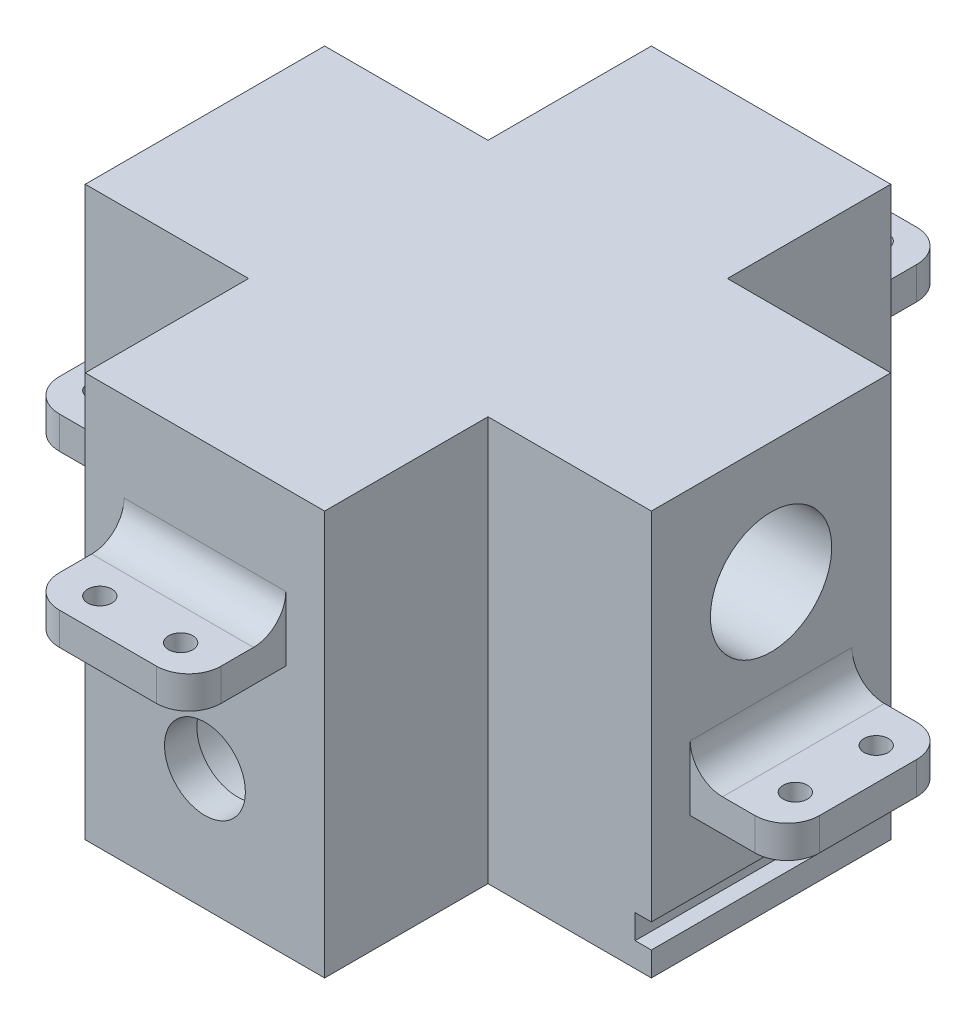
SolidWorks part; units mm, degrees
ref_plane "Plan de face" through (0, 0, 0) normal (0, 0, 1) x (1, 0, 0)
ref_plane "Plan de dessus" through (0, 0, 0) normal (0, 1, 0) x (1, 0, 0)
ref_plane "Plan de droite" through (0, 0, 0) normal (1, 0, 0) x (0, 0, -1)
sketch "Esquisse1" plane through (0, 0, 0) normal (1, 0, 0) x (0, 0, -1)
  line L2 (0, 0) -> (70, 0)
  line L3 (0, 0) -> (0, 50)
  line L4 (0, 50) -> (70, 50)
  line L5 (70, 0) -> (70, 50)
  dimension "D1" = 50
  dimension "D2" = 70
extrude "Boss.-Extru.1" add sketch "Esquisse1" along normal blind 70
sketch "Esquisse2" plane through (0, 0, 0) normal (0, 0, 1) x (1, 0, 0)
  line L0 (70, 0) -> (0, 0) construction
  line L1 (0, 50) -> (0, 0) construction
  circle A0 centre (35, 15) radius 7.5
  dimension "D1" = 15
  dimension "D2" = 15
  dimension "D3" = 35
extrude "Enlèv. mat.-Extru.1" cut sketch "Esquisse2" against normal through all
sketch "Esquisse3" plane through (0, 0, 0) normal (-1, 0, 0) x (0, 0, 1)
  line L0 (-70, 50) -> (0, 50) construction
  line L1 (0, 50) -> (0, 0) construction
  circle A0 centre (-35, 35) radius 7.5
  dimension "D1" = 15
  dimension "D2" = 15
  dimension "D3" = 35
extrude "Enlèv. mat.-Extru.2" cut sketch "Esquisse3" against normal through all
sketch "Esquisse4" plane through (0, 0, 0) normal (0, -1, 0) x (1, 0, 0)
  line L1 (0, -70) -> (20.2, -70)
  line L2 (0, -70) -> (0, -49.8)
  line L3 (0, -49.8) -> (20.2, -49.8)
  line L4 (20.2, -70) -> (20.2, -49.8)
  line L5 (0, 0) -> (20.2, 0)
  line L6 (0, 0) -> (0, -20.2)
  line L7 (0, -20.2) -> (20.2, -20.2)
  line L8 (20.2, 0) -> (20.2, -20.2)
  line L9 (70, 0) -> (49.8, 0)
  line L10 (70, 0) -> (70, -20.2)
  line L11 (70, -20.2) -> (49.8, -20.2)
  line L12 (49.8, 0) -> (49.8, -20.2)
  line L13 (70, -70) -> (49.8, -70)
  line L14 (70, -70) -> (70, -49.8)
  line L15 (70, -49.8) -> (49.8, -49.8)
  line L16 (49.8, -70) -> (49.8, -49.8)
  dimension "D1" = 20.2
  dimension "D2" = 20.2
  dimension "D3" = 20.2
  dimension "D4" = 20.2
  dimension "D5" = 20.2
  dimension "D6" = 20.2
  dimension "D7" = 20.2
  dimension "D8" = 20.2
extrude "Enlèv. mat.-Extru.3" cut sketch "Esquisse4" against normal through all
sketch "Esquisse7" plane through (0, 0, 0) normal (0, 0, 1) x (1, 0, 0)
  circle A0 centre (35, 15) radius 5
  circle A1 centre (35, 15) radius 11.7367
  dimension "D1" = 10
extrude "Boss.-Extru.3" add sketch "Esquisse7" against normal blind 4
sketch "Esquisse8" plane through (0, 0, 0) normal (-1, 0, 0) x (0, 0, 1)
  circle A0 centre (-35, 35) radius 12.1967
  circle A1 centre (-35, 35) radius 5
  dimension "D1" = 10
extrude "Boss.-Extru.4" add sketch "Esquisse8" against normal blind 4
sketch "Esquisse9" plane through (20.2, 0, 0) normal (-1, 0, 0) x (0, 0, 1)
  line L0 (-70, 50) -> (-70, 0) construction
  line L1 (-70, 6) -> (-68, 6)
  line L2 (-70, 6) -> (-70, 3)
  line L3 (-70, 3) -> (-68, 3)
  line L4 (-68, 6) -> (-68, 3)
  line L5 (-70, 0) -> (-49.8, 0) construction
  dimension "D1" = 3
  dimension "D2" = 3
  dimension "D3" = 2
extrude "Enlèv. mat.-Extru.4" cut sketch "Esquisse9" against normal through all
sketch "Esquisse10" plane through (0, 0, -49.8) normal (0, 0, -1) x (-1, 0, 0)
  line L0 (0, 50) -> (0, 0) construction
  line L1 (0, 3) -> (-2, 3)
  line L2 (0, 3) -> (0, 6)
  line L3 (0, 6) -> (-2, 6)
  line L4 (-2, 3) -> (-2, 6)
  line L5 (-20.2, 0) -> (0, 0) construction
  dimension "D1" = 3
  dimension "D2" = 2
  dimension "D3" = 3
extrude "Enlèv. mat.-Extru.5" cut sketch "Esquisse10" against normal through all
sketch "Esquisse11" plane through (0, 0, -49.8) normal (0, 0, -1) x (-1, 0, 0)
  line L0 (-70, 50) -> (-70, 0) construction
  line L1 (-70, 6) -> (-68, 6)
  line L2 (-70, 6) -> (-70, 3)
  line L3 (-70, 3) -> (-68, 3)
  line L4 (-68, 6) -> (-68, 3)
  line L5 (-70, 0) -> (-49.8, 0) construction
  dimension "D1" = 3
  dimension "D2" = 3
  dimension "D3" = 2
extrude "Enlèv. mat.-Extru.6" cut sketch "Esquisse11" against normal through all
sketch "Esquisse12" plane through (0, 0, 0) normal (-1, 0, 0) x (0, 0, 1)
  line L0 (-49.8, 50) -> (-49.8, 6) construction
  line L1 (-25, 15) -> (-45, 15)
  line L2 (-25, 15) -> (-25, 19)
  line L3 (-25, 19) -> (-45, 19)
  line L4 (-45, 15) -> (-45, 19)
  line L5 (-20.2, 50) -> (-20.2, 6) construction
  line L6 (-20.2, 0) -> (-49.8, 0) construction
  dimension "D1" = 4
  dimension "D2" = 20
  dimension "D3" = 4.8
  dimension "D4" = 4.8
  dimension "D5" = 15
extrude "Boss.-Extru.5" add sketch "Esquisse12" along normal blind 12
sketch "Esquisse13" plane through (0, 15, 0) normal (0, -1, 0) x (1, 0, 0)
  line L0 (0, -45) -> (0, -25) construction
  line L1 (-12, -45) -> (0, -45) construction
  line L2 (-12, -25) -> (0, -25) construction
  circle A0 centre (-8, -30) radius 1.5
  circle A1 centre (-8, -40) radius 1.5
  dimension "D1" = 3
  dimension "D2" = 3
  dimension "D3" = 8
  dimension "D4" = 8
  dimension "D5" = 10
  dimension "D6" = 5
  dimension "D7" = 5
extrude "Enlèv. mat.-Extru.7" cut sketch "Esquisse13" against normal through all
fillet "Congé1" radius 4 2 edges at (-12, 17, -25) (-12, 17, -45)
sketch "Esquisse14" plane through (70, 0, 0) normal (1, 0, 0) x (0, 0, -1)
  line L0 (49.8, 50) -> (49.8, 6) construction
  line L1 (45, 15) -> (25, 15)
  line L2 (45, 15) -> (45, 19)
  line L3 (45, 19) -> (25, 19)
  line L4 (25, 15) -> (25, 19)
  line L5 (20.2, 50) -> (20.2, 6) construction
  line L6 (20.2, 0) -> (49.8, 0) construction
  dimension "D1" = 4
  dimension "D2" = 20
  dimension "D3" = 4.8
  dimension "D4" = 4.8
  dimension "D5" = 15
extrude "Boss.-Extru.6" add sketch "Esquisse14" along normal blind 12
sketch "Esquisse15" plane through (0, 15, 0) normal (0, -1, 0) x (1, 0, 0)
  line L0 (82, -45) -> (70, -45) construction
  line L1 (70, -25) -> (70, -45) construction
  line L2 (82, -25) -> (70, -25) construction
  circle A0 centre (78, -40) radius 1.5
  circle A1 centre (78, -30) radius 1.5
  dimension "D1" = 3
  dimension "D2" = 3
  dimension "D3" = 10
  dimension "D4" = 5
  dimension "D5" = 8
  dimension "D6" = 5
extrude "Enlèv. mat.-Extru.8" cut sketch "Esquisse15" against normal through all
fillet "Congé3" radius 4 2 edges at (82, 17, -45) (82, 17, -25)
sketch "Esquisse16" plane through (0, 0, 0) normal (0, 0, 1) x (1, 0, 0)
  line L0 (49.8, 50) -> (20.2, 50) construction
  line L1 (45, 31) -> (25, 31)
  line L2 (45, 31) -> (45, 35)
  line L3 (45, 35) -> (25, 35)
  line L4 (25, 31) -> (25, 35)
  line L5 (20.2, 50) -> (20.2, 0) construction
  line L6 (49.8, 50) -> (49.8, 0) construction
  dimension "D1" = 20
  dimension "D2" = 4
  dimension "D3" = 15
  dimension "D4" = 4.8
  dimension "D5" = 4.8
extrude "Boss.-Extru.7" add sketch "Esquisse16" along normal blind 12
sketch "Esquisse17" plane through (0, 31, 0) normal (0, -1, 0) x (1, 0, 0)
  line L0 (25, 0) -> (45, 0) construction
  line L1 (25, 12) -> (25, 0) construction
  circle A0 centre (40, 8) radius 1.5
  circle A1 centre (30, 8) radius 1.5
  dimension "D1" = 3
  dimension "D2" = 3
  dimension "D3" = 10
  dimension "D4" = 8
  dimension "D5" = 8
  dimension "D6" = 5
extrude "Enlèv. mat.-Extru.9" cut sketch "Esquisse17" against normal through all
fillet "Congé4" radius 4 2 edges at (45, 33, 12) (25, 33, 12)
sketch "Esquisse18" plane through (0, 0, -70) normal (0, 0, -1) x (-1, 0, 0)
  line L0 (-49.8, 50) -> (-20.2, 50) construction
  line L1 (-25, 31) -> (-45, 31)
  line L2 (-25, 31) -> (-25, 35)
  line L3 (-25, 35) -> (-45, 35)
  line L4 (-45, 31) -> (-45, 35)
  line L5 (-20.2, 50) -> (-20.2, 6) construction
  line L6 (-49.8, 50) -> (-49.8, 6) construction
  point P4 (-35, 50)
  dimension "D1" = 4
  dimension "D2" = 20
  dimension "D3" = 15
  dimension "D4" = 4.8
  dimension "D5" = 4.8
extrude "Boss.-Extru.8" add sketch "Esquisse18" along normal blind 12
sketch "Esquisse19" plane through (0, 31, 0) normal (0, -1, 0) x (1, 0, 0)
  line L0 (45, -70) -> (25, -70) construction
  line L1 (25, -82) -> (25, -70) construction
  line L2 (45, -82) -> (45, -70) construction
  circle A0 centre (30, -78) radius 1.5
  circle A1 centre (40, -78) radius 1.5
  dimension "D1" = 3
  dimension "D2" = 3
  dimension "D3" = 10
  dimension "D4" = 8
  dimension "D5" = 8
  dimension "D6" = 5
  dimension "D7" = 5
extrude "Enlèv. mat.-Extru.10" cut sketch "Esquisse19" against normal through all
fillet "Congé5" radius 4 2 edges at (45, 33, -82) (25, 33, -82)
fillet "Congé6" radius 4 4 edges at (70, 19, -35) (35, 35, 0) (0, 19, -35) (35, 35, -70)
